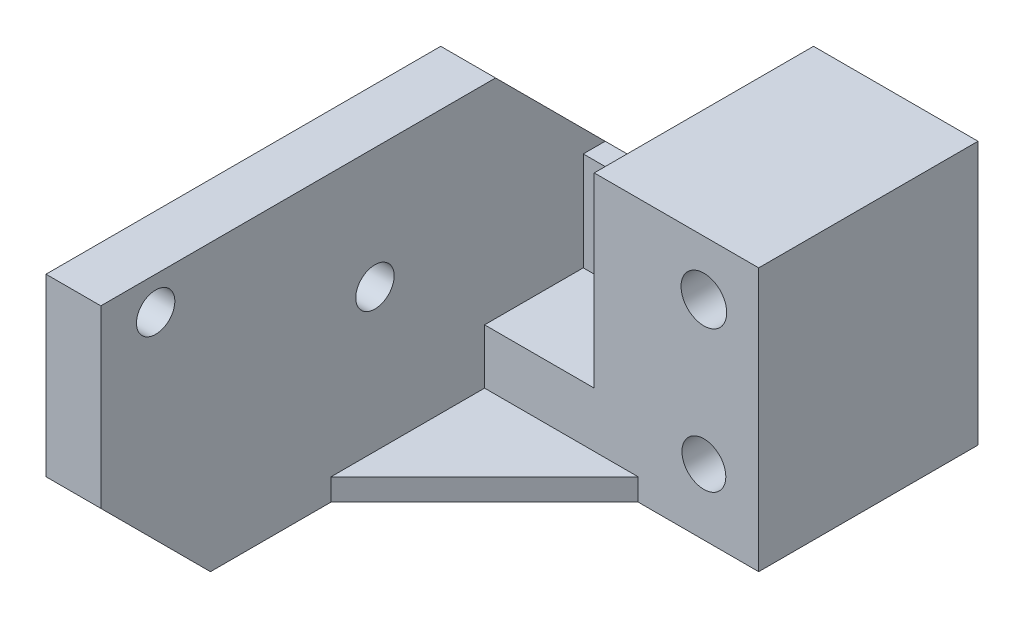
SolidWorks part; units mm, degrees
ref_plane "Спереди" through (0, 0, 0) normal (0, 0, 1) x (1, 0, 0)
ref_plane "Сверху" through (0, 0, 0) normal (0, 1, 0) x (1, 0, 0)
ref_plane "Справа" through (0, 0, 0) normal (1, 0, 0) x (0, 0, -1)
sketch "Эскиз1" plane through (0, 0, 0) normal (0, 1, 0) x (1, 0, 0)
  line L0 (0, 0) -> (0, 11)
  line L1 (0, 11) -> (15, 11)
  line L2 (15, 11) -> (15, 20)
  line L3 (15, 20) -> (30, 20)
  line L4 (30, 20) -> (30, 0)
  line L5 (30, 0) -> (0, 0)
  dimension "D1" = 20
  dimension "D2" = 9
  dimension "D3" = 15
  dimension "D4" = 15
extrude "Бобышка-Вытянуть1" add sketch "Эскиз1" along normal blind 12
sketch "Эскиз2" plane through (0, 0, 0) normal (0, 0, 1) x (1, 0, 0)
  line L0 (30, 6) -> (0, 6) construction
  line L1 (30, 12) -> (30, 0) construction
  line L2 (0, 12) -> (0, 0) construction
  circle A0 centre (25, 6) radius 2
  dimension "D1" = 5
  dimension "D2" = 4
extrude "Вырез-Вытянуть1" cut sketch "Эскиз2" against normal up to next
sketch "Эскиз3" plane through (0, 0, 0) normal (-1, 0, 0) x (0, 0, 1)
  line L0 (0, 12) -> (0, 0) construction
  line L1 (-11, 0) -> (35, 0)
  line L2 (-11, 0) -> (-11, 26)
  line L3 (-11, 26) -> (35, 26)
  line L4 (35, 0) -> (35, 26)
  line L5 (-11, 12) -> (0, 12) construction
  circle A0 centre (30, 23) radius 1.75
  circle A1 centre (10, 15) radius 1.75
  point P13 (6.2554, 14.5257)
  dimension "D3" = 3
  dimension "D6" = 5
  dimension "D7" = 3.5
  dimension "D1" = 35
  dimension "D2" = 14
  dimension "D4" = 3
  dimension "D5" = 10
extrude "Бобышка-Вытянуть2" add sketch "Эскиз3" against normal blind 5
chamfer "Фаска1" distance 10 angle 45 1 edges at (2.5, 26, -11)
sketch "Эскиз4" plane through (0, 0, 0) normal (0, -1, 0) x (1, 0, 0)
  line L0 (5, 14) -> (19, 0)
  line L1 (5, 0) -> (5, 35) construction
  line L2 (5, 0) -> (30, 0) construction
  line L3 (19, 0) -> (5, 0)
  line L4 (5, 0) -> (5, 14)
  dimension "D1" = 14
extrude "Бобышка-Вытянуть3" add sketch "Эскиз4" against normal blind 2
chamfer "Фаска2" distance 10 angle 45 1 edges at (2.5, 0, 35)
sketch "Эскиз5" plane through (0, 12, 0) normal (0, 1, 0) x (1, 0, 0)
  line L1 (15, 20) -> (30, 20)
  line L2 (15, 20) -> (15, 0)
  line L3 (15, 0) -> (30, 0)
  line L4 (30, 20) -> (30, 0)
extrude "Бобышка-Вытянуть4" add sketch "Эскиз5" along normal blind 12
sketch "Эскиз6" plane through (0, 0, 0) normal (0, 0, 1) x (1, 0, 0)
  line L0 (25, 19) -> (25, 6) construction
  line L3 (15, 24) -> (30, 24) construction
  circle A0 centre (25, 19) radius 2.0841
  dimension "D1" = 5
extrude "Вырез-Вытянуть2" cut sketch "Эскиз6" against normal through all
sketch "Эскиз7" plane through (0, 0, -11) normal (0, 0, -1) x (-1, 0, 0)
  line L0 (-15, 24) -> (-15, 0) construction
  line L1 (-15, 12) -> (-5, 12)
  line L2 (-15, 12) -> (-15, 7)
  line L3 (-15, 7) -> (-5, 7)
  line L4 (-5, 12) -> (-5, 7)
  point P6 (-5, 12)
  dimension "D1" = 5
extrude "Вырез-Вытянуть3" cut sketch "Эскиз7" against normal through all
sketch "Эскиз8" plane through (0, 0, -11) normal (0, 0, -1) x (-1, 0, 0)
  line L1 (-5, 16) -> (-15, 16)
  line L2 (-5, 16) -> (-5, 7)
  line L3 (-5, 7) -> (-15, 7)
  line L4 (-15, 16) -> (-15, 7)
extrude "Бобышка-Вытянуть5" add sketch "Эскиз8" against normal blind 2
chamfer "Фаска3" distance 4 angle 45 2 edges at (0, 8, -11) (7.5, 0, -11)
